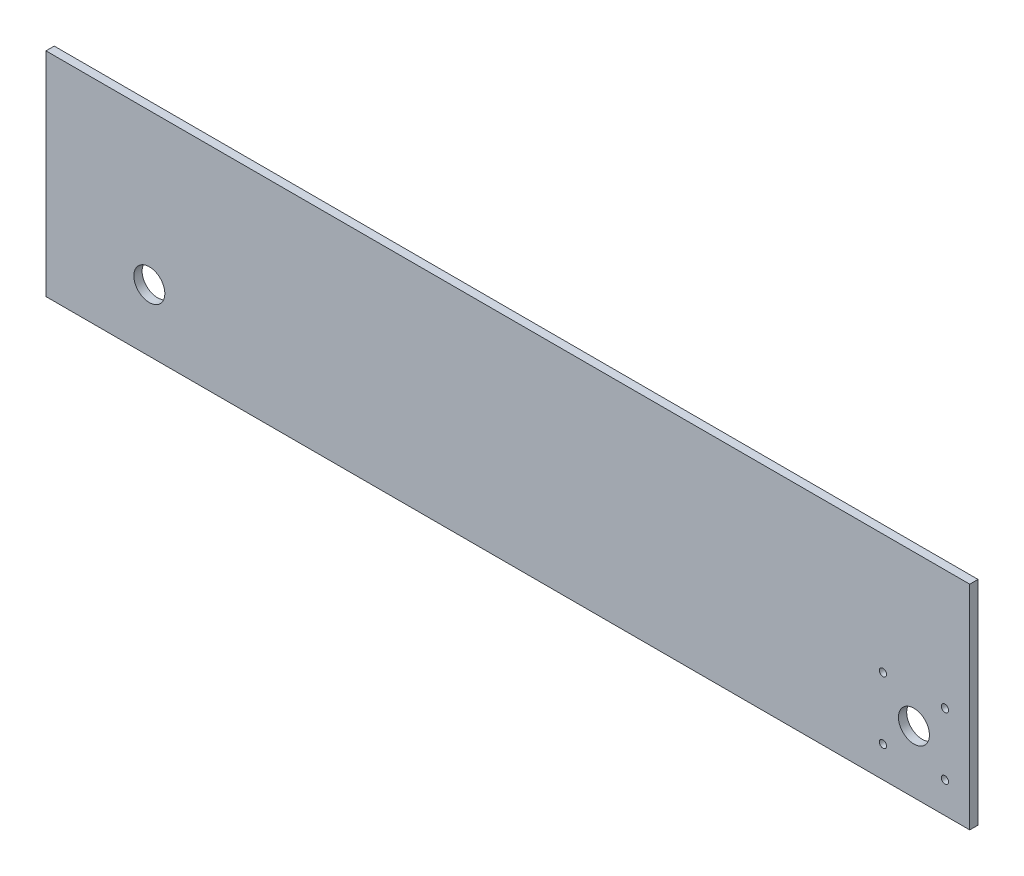
SolidWorks part; units mm, degrees
ref_plane "Front Plane" through (0, 0, 0) normal (0, 0, 1) x (1, 0, 0)
ref_plane "Top Plane" through (0, 0, 0) normal (0, 1, 0) x (1, 0, 0)
ref_plane "Right Plane" through (0, 0, 0) normal (1, 0, 0) x (0, 0, -1)
sketch "Sketch1" plane through (0, 0, 0) normal (0, 0, 1) x (1, 0, 0)
  line L1 (0, 0) -> (450, 0)
  line L2 (0, 0) -> (0, 103)
  line L3 (0, 103) -> (450, 103)
  line L4 (450, 0) -> (450, 103)
  dimension "D1" = 450
  dimension "D2" = 103
extrude "Boss-Extrude1" add sketch "Sketch1" along normal blind 4
sketch "Sketch6" plane through (0, 0, 4) normal (0, 0, 1) x (1, 0, 0)
  line L0 (0, 0) -> (450, 0) construction
  line L1 (0, 103) -> (0, 0) construction
  circle A0 centre (50, 30) radius 7.5
  dimension "D1" = 15
  dimension "D2" = 30
  dimension "D3" = 50
extrude "Cut-Extrude4" cut sketch "Sketch6" against normal through all
sketch "Sketch7" plane through (0, 0, 4) normal (0, 0, 1) x (1, 0, 0)
  line L0 (0, 0) -> (450, 0) construction
  line L1 (450, 0) -> (450, 103) construction
  circle A0 centre (420, 30) radius 7.5
  dimension "D1" = 15
  dimension "D2" = 30
  dimension "D3" = 30
extrude "Cut-Extrude5" cut sketch "Sketch7" against normal through all
sketch "Sketch8" plane through (0, 0, 4) normal (0, 0, 1) x (1, 0, 0)
  line L0 (274, 30) -> (290.4951, 30) construction
  line L1 (0, 0) -> (450, 0) construction
  line L2 (420, 50.7202) -> (420, 2.1415) construction
  line L3 (450, 0) -> (450, 103) construction
  circle A0 centre (435, 45) radius 1.75
  circle A2 centre (405, 45) radius 1.75
  circle A3 centre (405, 15) radius 1.75
  circle A4 centre (435, 15) radius 1.75
  dimension "D1" = 3.5
  dimension "D2" = 30
  dimension "D3" = 30
  dimension "D4" = 30
  dimension "D5" = 30
extrude "Cut-Extrude6" cut sketch "Sketch8" against normal through all
sketch "Sketch10" plane through (0, 0, 0) normal (0, 0, -1) x (-1, 0, 0)
  line L0 (0, 0) -> (-450, 0) construction
  line L1 (-450, 103) -> (-447, 103)
  line L2 (-450, 103) -> (-450, 0)
  line L3 (-450, 0) -> (-447, 0)
  line L4 (-447, 103) -> (-447, 0)
  line L5 (-447, 0) -> (-447, 3) construction
extrude "Cut-Extrude7" cut sketch "Sketch10" against normal blind 10
